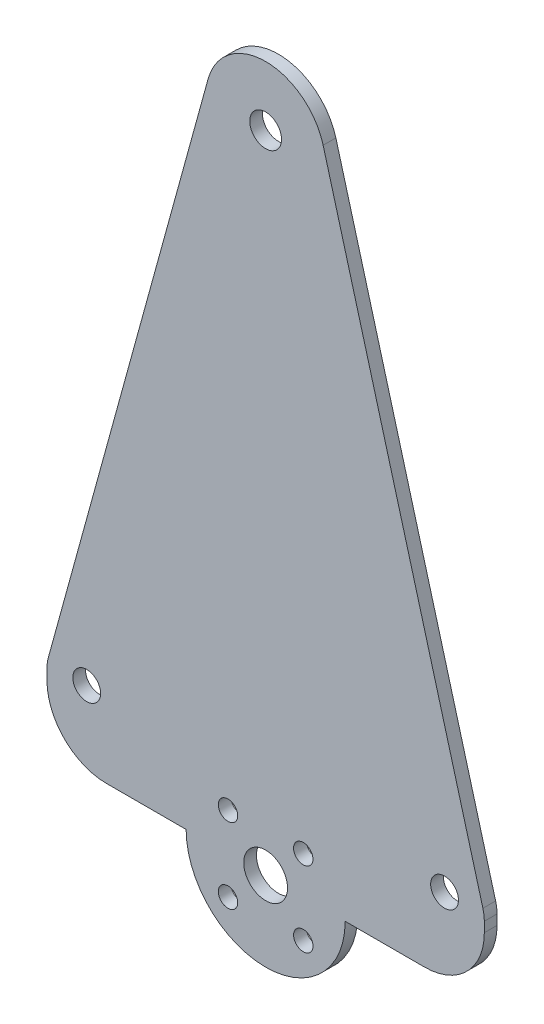
SolidWorks part; units mm, degrees
material "Acrylic (Medium-high impact)"
ref_plane "Front Plane" through (0, 0, 0) normal (0, 0, 1) x (1, 0, 0)
ref_plane "Top Plane" through (0, 0, 0) normal (0, 1, 0) x (1, 0, 0)
ref_plane "Right Plane" through (0, 0, 0) normal (1, 0, 0) x (0, 0, -1)
sketch "Sketch1" plane through (0, 0, 0) normal (0, 0, 1) x (1, 0, 0)
  line L0 (0, 0) -> (57.15, 0) construction
  line L1 (41.275, -11.9697) -> (53.975, -11.9697)
  line L2 (19.3909, 93.6034) -> (-6.1227, 0.8265)
  line L3 (63.5, -0.8572) -> (63.5, -2.4447)
  line L4 (15.875, -11.9697) -> (3.175, -11.9697)
  line L5 (-6.35, -2.4447) -> (-6.35, -0.8572)
  line L6 (63.2727, 0.8265) -> (37.7591, 93.6034)
  line L7 (28.575, 100.6028) -> (28.575, 0) construction
  line L8 (28.575, -11.9697) -> (34.5854, -17.9801) construction
  line L9 (28.575, -11.9697) -> (22.5646, -5.9593) construction
  line L10 (28.575, -11.9697) -> (22.5646, -17.9801) construction
  line L11 (28.575, -11.9697) -> (34.5854, -5.9593) construction
  circle A0 centre (0, 0) radius 2.2225
  circle A1 centre (57.15, 0) radius 2.2225
  arc A2 (-6.35, -0.8572) -> (-6.1227, 0.8265) centre (0, -0.8572) cw
  circle A3 centre (22.5646, -5.9593) radius 1.55
  arc A4 (53.975, -11.9697) -> (63.5, -2.4447) centre (53.975, -2.4447) ccw
  arc A5 (63.5, -0.8572) -> (63.2727, 0.8265) centre (57.15, -0.8572) ccw
  arc A6 (37.7591, 93.6034) -> (19.3909, 93.6034) centre (28.575, 91.0778) ccw
  circle A7 centre (28.575, 91.0778) radius 2.54
  arc A8 (15.875, -11.9697) -> (41.275, -11.9697) centre (28.575, -11.9697) ccw
  circle A9 centre (28.575, -11.9697) radius 3.5
  circle A10 centre (34.5854, -17.9801) radius 1.55
  arc A11 (-6.35, -2.4447) -> (3.175, -11.9697) centre (3.175, -2.4447) ccw
  circle A12 centre (34.5854, -5.9593) radius 1.55
  circle A13 centre (22.5646, -17.9801) radius 1.55
  point P17 (28.575, -11.9697)
  point P18 (-6.35, -11.9697)
  dimension "D1" = 4.445
  dimension "D2" = 4.445
  dimension "D6" = 6.35
  dimension "D7" = 9.525
  dimension "D9" = 9.525
  dimension "D8" = 5.08
  dimension "D10" = 12.7
  dimension "D11" = 7
  dimension "D13" = 3.1
  dimension "D5" = 9.525
  dimension "D15" = 3.1
  dimension "D16" = 3.1
  dimension "D17" = 3.1
  dimension "D3" = 57.15
  dimension "D4" = 11.1125
  dimension "D12" = 8.5
  dimension "D14" = 8.5
  dimension "D18" = 96.2211
extrude "Boss-Extrude1" add sketch "Sketch1" along normal blind 2.032
